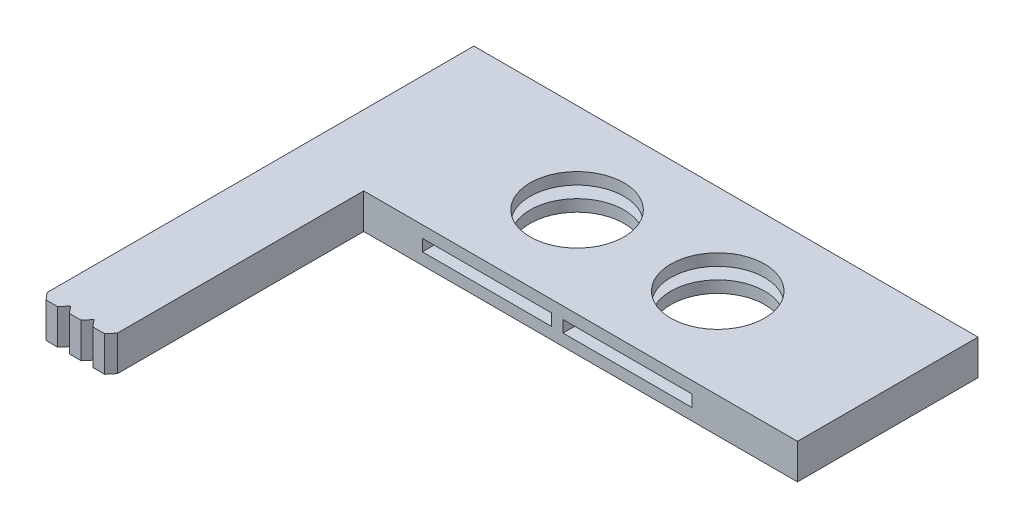
SolidWorks part; units mm, degrees
ref_plane "Front Plane" through (0, 0, 0) normal (0, 0, 1) x (1, 0, 0)
ref_plane "Top Plane" through (0, 0, 0) normal (0, 1, 0) x (1, 0, 0)
ref_plane "Right Plane" through (0, 0, 0) normal (1, 0, 0) x (0, 0, -1)
sketch "Sketch1" plane through (0, 0, 0) normal (0, 1, 0) x (1, 0, 0)
  line L0 (43, 7.7) -> (43, -7.7)
  line L1 (43, 7.7) -> (0, 7.7)
  line L2 (0, 7.7) -> (0, -28.7)
  line L5 (6, -7.7) -> (43, -7.7)
  line L6 (-47.7355, 0) -> (57.1135, 0) construction
  line L7 (0, -28.7) -> (0.5009, -29.3)
  line L8 (0.5009, -29.3) -> (1.4991, -29.3)
  line L9 (2, -28.7) -> (1.4991, -29.3)
  line L10 (1, -27.7079) -> (1, -29.6501) construction
  line L11 (2, -28.7) -> (2.5009, -29.3)
  line L12 (3, -27.7079) -> (3, -29.6501) construction
  line L13 (4, -28.7) -> (3.4991, -29.3)
  line L14 (4, -28.7) -> (4.5009, -29.3)
  line L15 (5, -27.7079) -> (5, -29.6501) construction
  line L16 (6, -28.7) -> (5.4991, -29.3)
  line L18 (7, -27.7079) -> (7, -29.6501) construction
  line L23 (2.5009, -29.3) -> (3.4991, -29.3)
  line L24 (4.5009, -29.3) -> (5.4991, -29.3)
  line L26 (8, -28.7) -> (7.4991, -29.3) [skipped]
  line L27 (6, -28.7) -> (6.5009, -29.3) [skipped]
  line L28 (6, -28.7) -> (6, -7.7)
  circle A0 centre (16.5, 0) radius 4
  circle A1 centre (28.5, 0) radius 4
  dimension "D5" = 8
  dimension "D1" = 15.4
  dimension "D2" = 10.5
  dimension "D3" = 43
  dimension "D4" = 37
  dimension "D6" = 12
  dimension "D7" = 0.6
  dimension "D9" = 2
  dimension "D10" = 4
extrude "Boss-Extrude1" add sketch "Sketch1" along normal blind 3
sketch "Sketch2" plane through (0, 0, 7.7) normal (0, 0, 1) x (1, 0, 0)
  line L0 (8, 1.5) -> (43, 1.5) construction
  line L1 (11, 2) -> (22, 2)
  line L2 (11, 2) -> (11, 1)
  line L3 (11, 1) -> (22, 1)
  line L4 (22, 2) -> (22, 1)
  line L5 (23, 2) -> (34, 2)
  line L6 (23, 2) -> (23, 1)
  line L7 (23, 1) -> (34, 1)
  line L8 (34, 2) -> (34, 1)
  line L13 (16.5, 3.4489) -> (16.5, -1.3527) construction
  line L14 (43, 3) -> (43, 0) construction
  line L15 (12.5, 3) -> (12.5, 0) construction
  line L16 (20.5, 0) -> (20.5, 3) construction
  line L17 (28.5, 3.4489) -> (28.5, -1.3527) construction
  line L18 (24.5, 3) -> (24.5, 0) construction
  line L19 (32.5, 0) -> (32.5, 3) construction
  dimension "D1" = 11
  dimension "D2" = 11
  dimension "D3" = 1
extrude "Cut-Extrude1" cut sketch "Sketch2" against normal offset from surface (13.4 mm away) 2 up to face at (21.5, 1.5, -7.7)
